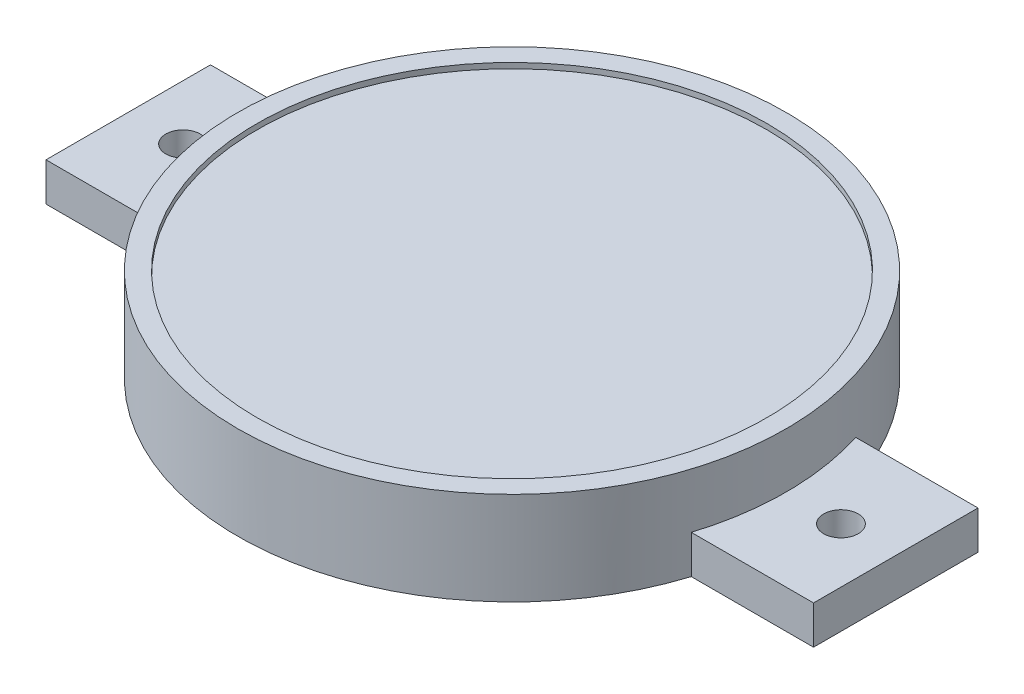
SolidWorks part; units mm, degrees
ref_plane "Front Plane" through (0, 0, 0) normal (0, 0, 1) x (1, 0, 0)
ref_plane "Top Plane" through (0, 0, 0) normal (0, 1, 0) x (1, 0, 0)
ref_plane "Right Plane" through (0, 0, 0) normal (1, 0, 0) x (0, 0, -1)
sketch "Sketch1" plane through (0, 0, 0) normal (0, 1, 0) x (1, 0, 0)
  circle A0 centre (0, 0) radius 50
  dimension "D1" = 100
extrude "Boss-Extrude1" add sketch "Sketch1" along normal blind 16
sketch "Sketch2" plane through (0, 16, 0) normal (0, 1, 0) x (1, 0, 0)
  circle A1 centre (0, 0) radius 46.5
  circle A2 centre (0, 0) radius 50
  circle A3 centre (0, 0) radius 50
  dimension "D2" = 93
  dimension "D1" = 0
extrude "Boss-Extrude2" add sketch "Sketch2" along normal blind 1
sketch "Sketch3" plane through (0, 0, 0) normal (0, -1, 0) x (1, 0, 0)
  circle A0 centre (0, 0) radius 47
  circle A1 centre (0, 0) radius 50 construction
  dimension "D1" = 3
extrude "Cut-Extrude1" cut sketch "Sketch3" against normal blind 10
sketch "Sketch4" plane through (0, 0, 0) normal (0, 1, 0) x (1, 0, 0)
  line L0 (-47.697, 15) -> (-70, 15)
  line L1 (-70, 15) -> (-70, -15)
  line L2 (-70, 0) -> (-50, 0) construction
  line L3 (0, 0) -> (0, 17.9128) construction
  line L4 (-47.697, -15) -> (-70, -15)
  line L5 (70, 0) -> (50, 0) construction
  line L6 (47.697, -15) -> (70, -15)
  line L7 (70, 15) -> (70, -15)
  line L8 (47.697, 15) -> (70, 15)
  arc A0 (-47.697, -15) -> (-47.697, 15) centre (0, 0) cw
  circle A1 centre (60, 0) radius 3.15
  circle A2 centre (0, 0) radius 50 construction
  circle A3 centre (-60, 0) radius 3.15
  arc A4 (47.697, -15) -> (47.697, 15) centre (0, 0) ccw
  dimension "D3" = 6.3
  dimension "D1" = 30
  dimension "D2" = 20
extrude "Boss-Extrude3" add sketch "Sketch4" along normal blind 7
